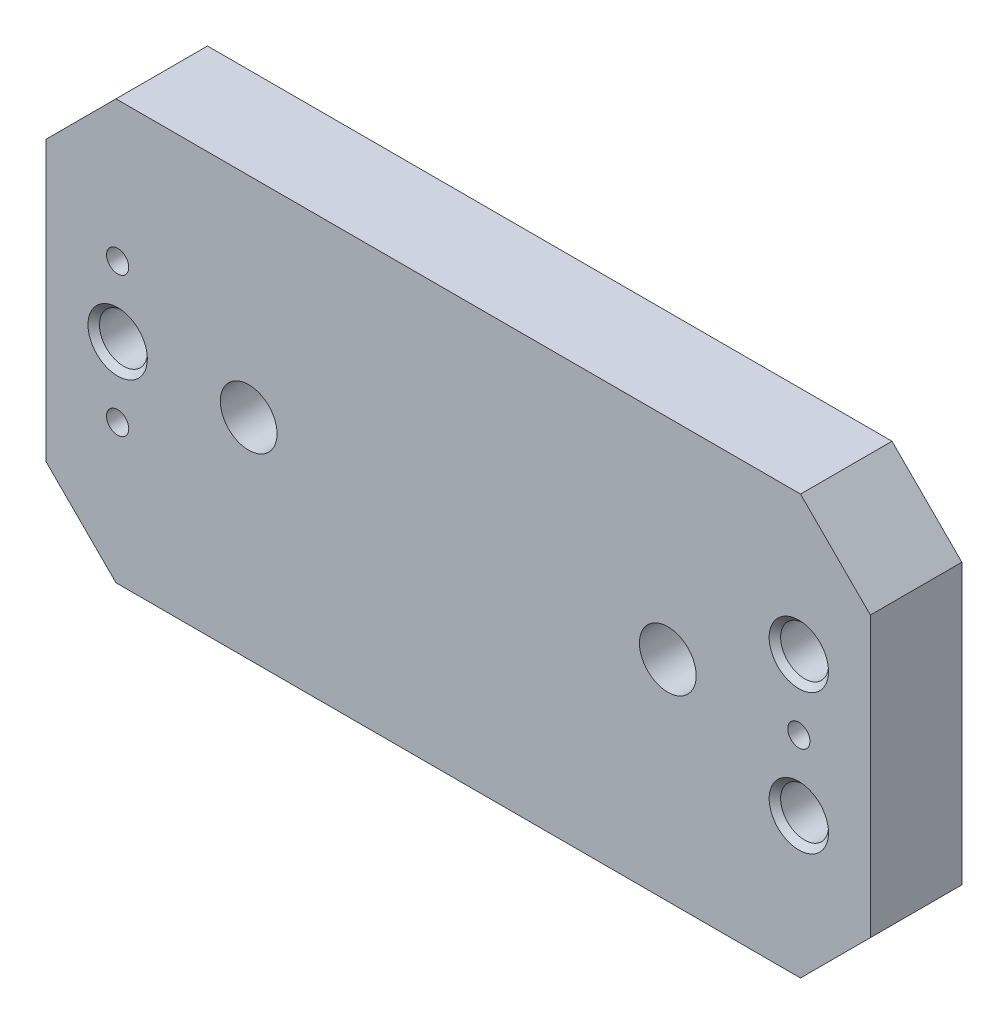
SolidWorks part; units mm, degrees
material "6061-T6 Al"
ref_plane "Front Plane" through (0, 0, 0) normal (0, 0, 1) x (1, 0, 0)
ref_plane "Top Plane" through (0, 0, 0) normal (0, 1, 0) x (1, 0, 0)
ref_plane "Right Plane" through (0, 0, 0) normal (1, 0, 0) x (0, 0, -1)
sketch "Sketch1" plane through (0, 0, 0) normal (0, 0, 1) x (1, 0, 0)
  line L0 (0, 0) -> (0, -38.1) construction
  line L1 (74.93, -38.1) -> (-74.93, -38.1)
  line L2 (74.93, -38.1) -> (74.93, 38.1)
  line L3 (74.93, 38.1) -> (-74.93, 38.1)
  line L4 (-74.93, -38.1) -> (-74.93, 38.1)
  line L5 (0, 0) -> (-74.93, 0) construction
  dimension "D1" = 149.86
  dimension "D2" = 76.2
extrude "Extrude1" add sketch "Sketch1" along normal blind 17.399
sketch "Sketch2" plane through (0, 0, 0) normal (0, 0, -1) x (-1, 0, 0)
  line L0 (-74.93, 38.1) -> (74.93, 38.1) construction
  line L1 (-74.93, -38.1) -> (74.93, -38.1)
  line L2 (-74.93, -38.1) -> (-74.93, 38.1)
  line L3 (-74.93, 38.1) -> (74.93, 38.1)
  line L4 (74.93, -38.1) -> (74.93, 38.1)
  line L5 (74.93, -38.1) -> (-74.93, -38.1) construction
  line L6 (-74.93, -38.1) -> (-74.93, 38.1) construction
  line L7 (74.93, 38.1) -> (74.93, -38.1) construction
  line L8 (0, 0) -> (-52.4002, 0) construction
  line L9 (-71.4502, -19.05) -> (-52.4002, -19.05)
  line L10 (-71.4502, -19.05) -> (-71.4502, 19.05)
  line L11 (-71.4502, 19.05) -> (-52.4002, 19.05)
  line L12 (-52.4002, -19.05) -> (-52.4002, 19.05)
  line L13 (52.4002, -19.05) -> (71.4502, -19.05)
  line L14 (52.4002, -19.05) -> (52.4002, 19.05)
  line L15 (52.4002, 19.05) -> (71.4502, 19.05)
  line L16 (71.4502, -19.05) -> (71.4502, 19.05)
  line L17 (0, 0) -> (52.4002, 0) construction
  dimension "D1" = 19.05
  dimension "D2" = 52.4002
  dimension "D3" = 38.1
extrude "Cut-Extrude1" cut sketch "Sketch2" against normal blind 0.762
hole_wizard "#10-32 Tapped Hole1" positions "Sketch4" profile "Sketch3" tap size "#10-32" standard "Ansi Inch" end condition through all
sketch "Sketch4" plane through (0, 0, 17.399) normal (0, 0, 1) x (1, 0, 0)
  line L0 (0, 0) -> (61.9252, 0) construction
  point P0 (61.9252, 0)
  point P1 (-61.9252, -12.7)
  point P9 (-61.9252, 12.7)
  dimension "D1" = 61.9252
  dimension "D2" = 12.7
  dimension "D3" = 61.9252
  dimension "D4" = 61.9252
  dimension "D5" = 12.7
sketch "Sketch3" plane through (61.9252, 0, 17.399) normal (1, 0, 0) x (0, -1, 0)
  line L0 (0, 0) -> (0, 17.399)
  line L1 (0, 17.399) -> (2.0193, 17.399)
  line L2 (2.0193, 17.399) -> (2.0193, 0)
  line L5 (2.0193, 0) -> (0, 0)
  line L11 (0, -6.35) -> (0, 107.95) construction
  dimension "Thru Tap Drill Dia." = 4.0386
  dimension "Thru Tap Drill Depth" = 17.399
cosmetic thread "Hole Thread1" parameters "D2"=4.826
cosmetic thread "Hole Thread2" parameters "D2"=4.826
cosmetic thread "Hole Thread4" parameters "D2"=4.826
hole_wizard "CBORE for #10 Socket Head Cap Screw1" positions "Sketch6" profile "Sketch5" counterbore size "#10" standard "Ansi Inch" end condition through all
sketch "Sketch6" plane through (0, 0, 17.399) normal (0, 0, 1) x (1, 0, 0)
  line L0 (61.9252, 0) -> (61.9252, -12.7) construction
  line L2 (61.9252, 0) -> (61.9252, 12.7) construction
  line L3 (61.9252, 0) -> (-61.9252, 0) construction
  line L4 (-61.9252, -12.7) -> (-61.9252, 0) construction
  point P0 (61.9252, -12.7)
  point P1 (61.9252, 12.7)
  point P10 (-61.9252, 0)
  dimension "D1" = 12.7
sketch "Sketch5" plane through (61.9252, -12.7, 17.399) normal (1, 0, 0) x (0, -1, 0)
  line L0 (0, 0) -> (0, 17.399)
  line L1 (0, 17.399) -> (2.8067, 17.399)
  line L3 (2.8067, 17.399) -> (2.8067, 15.0368)
  line L4 (4.3561, 15.0368) -> (2.8067, 15.0368)
  line L5 (4.3561, 15.0368) -> (4.3561, 1.0414)
  line L6 (4.3561, 1.0414) -> (5.3975, 0)
  line L7 (5.3975, 0) -> (0, 0)
  line L8 (-4.3561, 1.0414) -> (-5.3975, 0) construction
  line L11 (0, -6.35) -> (0, 107.95) construction
  dimension "Thru Hole Dia." = 5.6134
  dimension "Thru Hole Depth" = 17.399
  dimension "C'Bore Dia." = 8.7122
  dimension "C'Bore Depth" = 15.0368
  dimension "Near C'Sink Dia." = 10.795
  dimension "Near C'Sink Angle" = 90
chamfer "Chamfer1" distance 12.7 angle 45 4 edges at (-74.93, -38.1, 9.0805) (-74.93, 38.1, 9.0805) (74.93, -38.1, 9.0805) (74.93, 38.1, 9.0805)
sketch "Sketch7" plane through (0, 0, 0) normal (0, 0, -1) x (-1, 0, 0)
  line L0 (61.9252, -12.7) -> (61.9252, -19.05) construction
  line L1 (62.7126, -19.05) -> (61.1378, -19.05)
  line L2 (62.7126, -19.05) -> (62.7126, 19.05)
  line L3 (62.7126, 19.05) -> (61.1378, 19.05)
  line L4 (61.1378, -19.05) -> (61.1378, 19.05)
  line L5 (-61.1378, -19.05) -> (-62.7126, -19.05)
  line L6 (-61.1378, -19.05) -> (-61.1378, 19.05)
  line L7 (-61.1378, 19.05) -> (-62.7126, 19.05)
  line L8 (-62.7126, -19.05) -> (-62.7126, 19.05)
  line L9 (52.4002, -19.05) -> (71.4502, -19.05) construction
  line L10 (71.4502, 19.05) -> (52.4002, 19.05) construction
  line L11 (-61.9252, -12.7) -> (-61.9252, -19.05) construction
  line L13 (-71.4502, -19.05) -> (-52.4002, -19.05) construction
  line L14 (-52.4002, 19.05) -> (-71.4502, 19.05) construction
  dimension "D1" = 1.5748
extrude "Cut-Extrude2" cut sketch "Sketch7" against normal up to surface (0.762 mm away) up to face at (-61.9252, 0, 0.762)
hole_wizard "13/32 (0.40625) Diameter Hole1" positions "Sketch9" profile "Sketch8" hole size "13/32" standard "Ansi Inch" end condition through all
sketch "Sketch9" plane through (0, 0, 17.399) normal (0, 0, 1) x (1, 0, 0)
  line L0 (0, 0) -> (38.1, 0) construction
  line L1 (0, 0) -> (-38.1, 0) construction
  point P0 (-38.1, 0)
  point P1 (38.1, 0)
  dimension "D1" = 38.1
sketch "Sketch8" plane through (-38.1, 0, 17.399) normal (1, 0, 0) x (0, -1, 0)
  line L0 (0, 0) -> (0, 17.399)
  line L1 (0, 17.399) -> (5.1594, 17.399)
  line L2 (5.1594, 17.399) -> (5.1594, 0)
  line L5 (5.1594, 0) -> (0, 0)
  line L11 (0, -6.35) -> (0, 107.95) construction
  dimension "Thru Hole Dia." = 10.3187
  dimension "Thru Hole Depth" = 17.399
